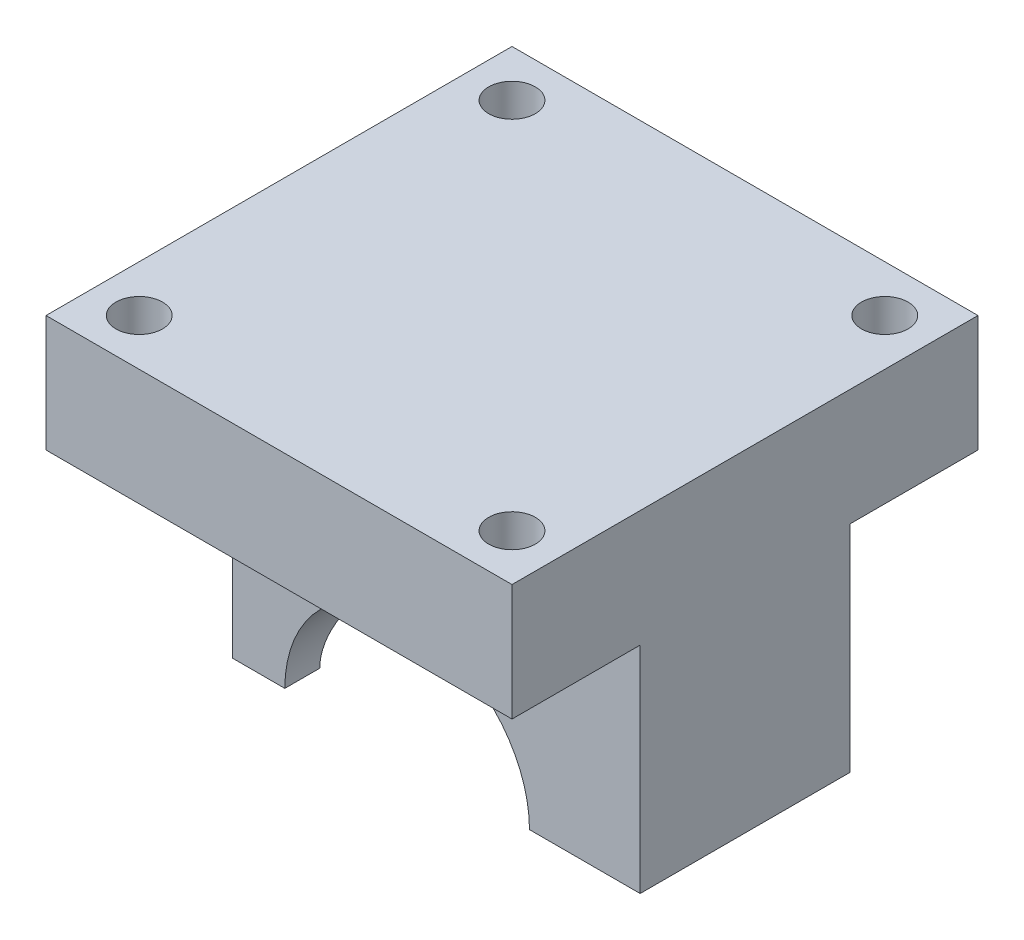
SolidWorks part; units mm, degrees
ref_plane "Front" through (0, 0, 0) normal (0, 0, 1) x (1, 0, 0)
ref_plane "Top" through (0, 0, 0) normal (0, 1, 0) x (1, 0, 0)
ref_plane "Right" through (0, 0, 0) normal (1, 0, 0) x (0, 0, -1)
sketch "Sketch1" plane through (0, 0, 0) normal (0, 1, 0) x (1, 0, 0)
  line L1 (-20, -9) -> (20, -9)
  line L2 (-20, -9) -> (-20, 9)
  line L3 (-20, 9) -> (20, 9)
  line L4 (20, -9) -> (20, 9)
  line L5 (-20, -9) -> (20, 9) construction
  line L6 (-20, 9) -> (20, -9) construction
  point P0 (0, 0)
  dimension "D1" = 40
  dimension "D2" = 18
extrude "Boss-Extrude1" add sketch "Sketch1" along normal blind 18.47
sketch "Sketch2" plane through (0, 0, 9) normal (0, 0, 1) x (1, 0, 0)
  line L0 (0, 0) -> (0, 18.47) construction
  line L1 (-20, 18.47) -> (20, 18.47) construction
  line L2 (-20, 0) -> (10, 0) construction
  line L3 (-20, 0) -> (20, 0) construction
  circle A0 centre (0, 0) radius 10.5
  dimension "D1" = 21
extrude "Cut-Extrude1" cut sketch "Sketch2" against normal up to next
sketch "Sketch4" plane through (-20, 0, 0) normal (-1, 0, 0) x (0, 0, 1)
  line L0 (-9, 0) -> (9, 0) construction
  circle A0 centre (0, 0) radius 6
  dimension "D1" = 12
extrude "Cut-Extrude3" cut sketch "Sketch4" against normal up to next
sketch "Sketch5" plane through (0, 0, 0) normal (0, -1, 0) x (1, 0, 0)
  line L0 (-10.5, -9) -> (-20, -9) construction
  line L1 (-15, 9) -> (-20, 9)
  line L2 (-15, 9) -> (-15, -9)
  line L3 (-15, -9) -> (-20, -9)
  line L4 (-20, 9) -> (-20, -9)
  line L5 (-15, 9) -> (-20, -9) construction
  line L6 (-15, -9) -> (-20, 9) construction
  line L7 (-20, -9) -> (-20, -6) construction
  point P0 (-17.5, 0)
  dimension "D1" = 0
  dimension "D2" = 0
  dimension "D3" = 5
  dimension "D4" = 0
extrude "Cut-Extrude4" cut sketch "Sketch5" against normal up to next
sketch "Sketch6" plane through (0, 18.47, 0) normal (0, 1, 0) x (1, 0, 0)
  line L0 (20, -9) -> (20, 9) construction
  line L1 (-20, -20) -> (20, -20)
  line L2 (-20, -20) -> (-20, 20)
  line L3 (-20, 20) -> (20, 20)
  line L4 (20, -20) -> (20, 20)
  line L5 (-20, -20) -> (20, 20) construction
  line L6 (-20, 20) -> (20, -20) construction
  point P0 (0, 0)
  dimension "D1" = 0
  dimension "D2" = 40
extrude "Boss-Extrude2" add sketch "Sketch6" along normal blind 10
sketch "Sketch7" plane through (0, 18.47, 0) normal (0, -1, 0) x (1, 0, 0)
  line L0 (-20, 20) -> (20, 20) construction
  line L1 (20, 20) -> (20, 9) construction
  circle A0 centre (16, 16) radius 2
  circle A1 centre (-16, 16) radius 2
  circle A2 centre (16, -16) radius 2
  circle A3 centre (-16, -16) radius 2
  dimension "D1" = 4
  dimension "D2" = 4
  dimension "D3" = 4
  dimension "D4" = 2
  dimension "D5" = 2
extrude "Cut-Extrude5" cut sketch "Sketch7" against normal up to next
